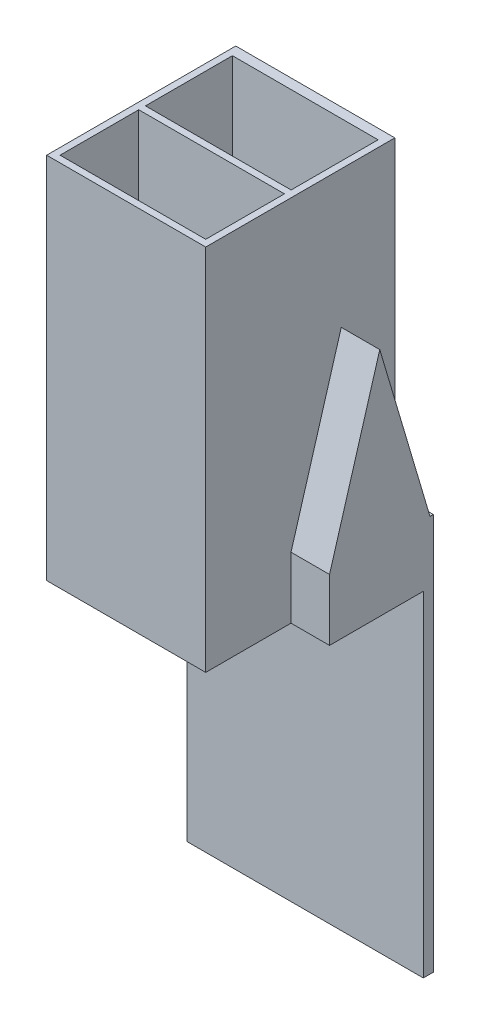
SolidWorks part; units mm, degrees
ref_plane "Ebene vorne" through (0, 0, 0) normal (0, 0, 1) x (1, 0, 0)
ref_plane "Ebene oben" through (0, 0, 0) normal (0, 1, 0) x (1, 0, 0)
ref_plane "Ebene rechts" through (0, 0, 0) normal (1, 0, 0) x (0, 0, -1)
sketch "Skizze1" plane through (0, 0, 0) normal (0, 1, 0) x (1, 0, 0)
  line L0 (0.4, 0.4) -> (0.4, 5.1)
  line L1 (0, 0) -> (9.5, 0)
  line L2 (0, 0) -> (0, 11.093)
  line L3 (0, 11.093) -> (9.5, 11.093)
  line L4 (9.5, 0) -> (9.5, 11.093)
  line L9 (0.4, 10.693) -> (9.1, 10.693)
  line L10 (9.1, 0.4) -> (9.1, 5.1)
  line L11 (0.4, 0.4) -> (9.1, 0.4)
  line L12 (0.4, 5.1) -> (9.1, 5.1)
  line L13 (9.1, 5.5) -> (0.4, 5.5)
  line L14 (0.4, 5.5) -> (0.4, 10.693)
  line L15 (0.4, 0.4) -> (0.4, 10.693) construction
  line L16 (9.1, 5.5) -> (9.1, 10.693)
  line L17 (9.1, 0.4) -> (9.1, 10.693) construction
  dimension "D1" = 11.093
  dimension "D2" = 9.5
  dimension "D3" = 0.4
  dimension "D4" = 0.4
  dimension "D5" = 5.193
extrude "Aufsatz-Linear austragen1" add sketch "Skizze1" along normal blind 22
sketch "Skizze2" plane through (0, 0, 0) normal (-1, 0, 0) x (0, 0, 1)
  line L0 (-11.093, 0) -> (-11.093, 3.67)
  line L1 (-11.093, 22) -> (-11.093, 0) construction
  line L2 (-11.093, 3.67) -> (-8.093, 13.8)
  line L3 (-8.093, 13.8) -> (-5.093, 3.67)
  line L4 (-5.093, 3.67) -> (-5.093, 0)
  line L5 (-11.093, 0) -> (0, 0) construction
  line L6 (-5.093, 0) -> (-11.093, 0)
  dimension "D1" = 3.67
  dimension "D2" = 6
  dimension "D3" = 3
  dimension "D4" = 13.8
extrude "Aufsatz-Linear austragen2" add sketch "Skizze2" along normal blind 2.3
ref_plane "Ebene1" through (4.75, 0, 0) normal (1, 0, 0) x (0, 0, -1)
mirror "Spiegeln1" about plane through (4.75, 0, 0) normal (1, 0, 0) of "Aufsatz-Linear austragen2"
sketch "Skizze3" plane through (-2.3, 0, 0) normal (-1, 0, 0) x (0, 0, 1)
  line L23 (-10.693, 0.4) -> (-5.493, 0.4)
  line L24 (-10.693, 3.612) -> (-10.693, 0.4)
  line L25 (-5.493, 0.4) -> (-5.493, 3.612)
  line L26 (-5.493, 3.612) -> (-8.093, 12.3913)
  line L27 (-8.093, 12.3913) -> (-10.693, 3.612)
  line L28 (-10.693, 0.4) -> (-5.493, 0.4)
  line L29 (-10.693, 3.612) -> (-10.693, 0.4)
  line L30 (-5.493, 0.4) -> (-5.493, 3.612)
  line L31 (-5.493, 3.612) -> (-8.093, 12.3913)
  line L32 (-8.093, 12.3913) -> (-10.693, 3.612)
  dimension "D1" = 0.4
extrude "Schnitt-Linear austragen1" cut sketch "Skizze3" against normal blind 13.7
sketch "Skizze4" plane through (0, 0, 0) normal (0, -1, 0) x (1, 0, 0)
  line L0 (9.1, -10.693) -> (0.4, -10.693) construction
  line L1 (-1.9, -5.5) -> (11.4, -5.5)
  line L2 (-1.9, -5.5) -> (-1.9, -10.693)
  line L3 (-1.9, -10.693) -> (11.4, -10.693)
  line L4 (11.4, -5.5) -> (11.4, -10.693)
  line L5 (0.4, -5.5) -> (9.1, -5.5) construction
  line L6 (-2.3, -11.093) -> (-2.3, -5.093) construction
  line L7 (11.8, -11.093) -> (11.8, -5.093) construction
  dimension "D1" = 0.4
  dimension "D2" = 0.4
extrude "Schnitt-Linear austragen2" cut sketch "Skizze4" against normal blind 0.4
sketch "Skizze5" plane through (0, 0, 0) normal (0, -1, 0) x (1, 0, 0)
  line L0 (11.8, -11.093) -> (11.8, -5.093) construction
  line L1 (-2.3, -11.093) -> (11.8, -11.093)
  line L2 (-2.3, -11.093) -> (-2.3, -10.693)
  line L3 (-2.3, -10.693) -> (11.8, -10.693)
  line L4 (11.8, -11.093) -> (11.8, -10.693)
  line L5 (11.4, -10.693) -> (-1.9, -10.693) construction
extrude "Aufsatz-Linear austragen3" add sketch "Skizze5" along normal blind 20
sketch "Skizze6" plane through (0, 0, -11.093) normal (0, 0, -1) x (-1, 0, 0)
  line L0 (0, 3.67) -> (2.3, 3.67)
  line L1 (-11.8, -20) -> (2.3, -20)
  line L2 (-11.8, -20) -> (-11.8, 3.67)
  line L3 (-11.8, 3.67) -> (-9.5, 3.67)
  line L4 (2.3, -20) -> (2.3, 3.67)
  line L5 (-9.5, 22) -> (0, 22)
  line L6 (-9.5, 22) -> (-9.5, 3.67)
  line L8 (0, 22) -> (0, 3.67)
extrude "Aufsatz-Linear austragen4" add sketch "Skizze6" along normal blind 0.2
